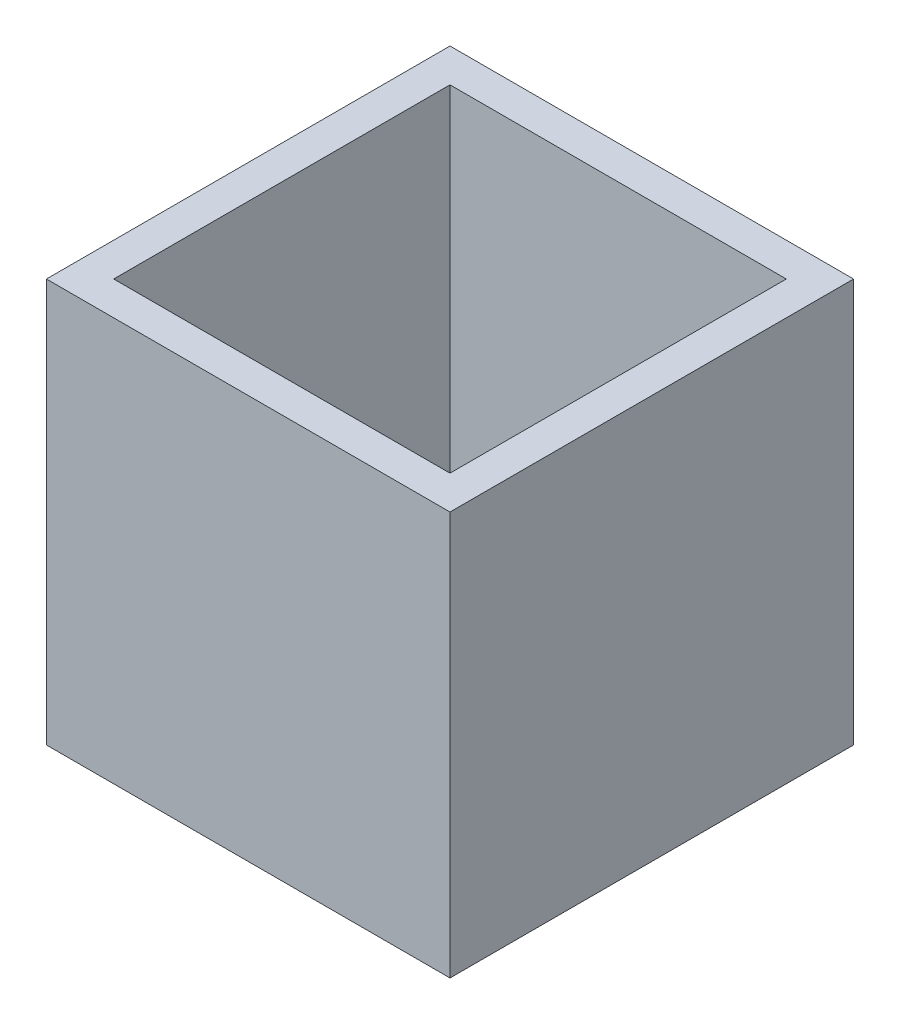
SolidWorks part; units mm, degrees
ref_plane "Front Plane" through (0, 0, 0) normal (0, 0, 1) x (1, 0, 0)
ref_plane "Top Plane" through (0, 0, 0) normal (0, 1, 0) x (1, 0, 0)
ref_plane "Right Plane" through (0, 0, 0) normal (1, 0, 0) x (0, 0, -1)
sketch "Sketch1" plane through (0, 0, 0) normal (0, 1, 0) x (1, 0, 0)
  line L1 (-150, -150) -> (150, -150)
  line L2 (-150, -150) -> (-150, 150)
  line L3 (-150, 150) -> (150, 150)
  line L4 (150, -150) -> (150, 150)
  line L5 (-150, -150) -> (150, 150) construction
  line L6 (-150, 150) -> (150, -150) construction
  point P0 (0, 0)
  dimension "D1" = 300
  dimension "D2" = 300
extrude "Extrude1" add sketch "Sketch1" along normal blind 300
shell "Shell1" thickness 25
